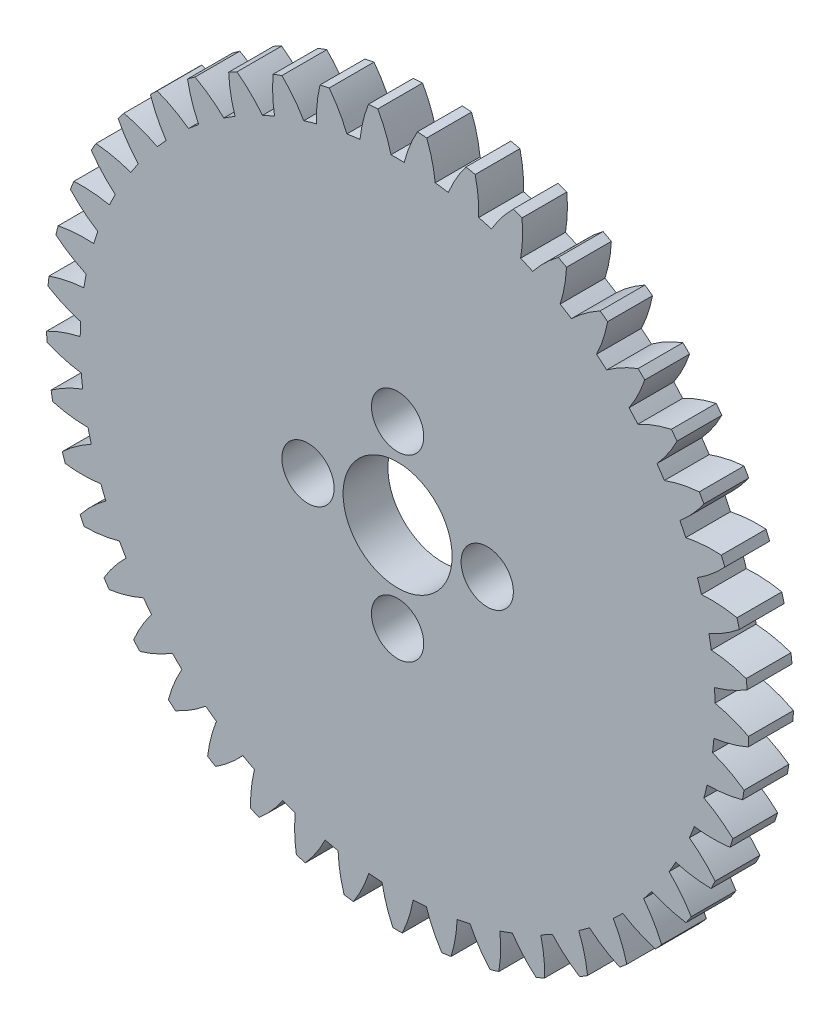
SolidWorks part; units mm, degrees
ref_plane "Front Plane" through (0, 0, 0) normal (0, 0, 1) x (1, 0, 0)
ref_plane "Top Plane" through (0, 0, 0) normal (0, 1, 0) x (1, 0, 0)
ref_plane "Right Plane" through (0, 0, 0) normal (1, 0, 0) x (0, 0, -1)
sketch "Model" plane through (0, 0, 0) normal (0, 0, 1) x (1, 0, 0)
  circle A0 centre (55.7791, 90.651) radius 15.95 construction
  arc A1 (32.4426, 93.4186) -> (32.3772, 92.7957) centre (55.7791, 90.651) ccw
  arc A2 (34.7806, 93.9041) -> (32.4426, 93.4186) centre (35.4255, 84.9273) ccw
  arc A3 (34.9343, 94.7759) -> (34.7806, 93.9041) centre (55.7791, 90.651) ccw
  arc A4 (32.9034, 96.0318) -> (34.9343, 94.7759) centre (38.6106, 102.9908) ccw
  arc A5 (33.0549, 96.6395) -> (32.9034, 96.0318) centre (55.7791, 90.651) ccw
  arc A6 (35.4377, 96.7949) -> (33.0549, 96.6395) centre (34.827, 87.8157) ccw
  arc A7 (35.7112, 97.6368) -> (35.4377, 96.7949) centre (55.7791, 90.651) ccw
  arc A8 (33.8749, 99.1631) -> (35.7112, 97.6368) centre (40.495, 105.2601) ccw
  arc A9 (34.1095, 99.7438) -> (33.8749, 99.1631) centre (55.7791, 90.651) ccw
  arc A10 (36.4907, 99.5661) -> (34.1095, 99.7438) centre (34.6363, 90.7592) ccw
  arc A11 (36.8788, 100.3617) -> (36.4907, 99.5661) centre (55.7791, 90.651) ccw
  arc A12 (35.2727, 102.1287) -> (36.8788, 100.3617) centre (42.677, 107.2451) ccw
  arc A13 (35.5859, 102.6711) -> (35.2727, 102.1287) centre (55.7791, 90.651) ccw
  arc A14 (37.9192, 102.1637) -> (35.5859, 102.6711) centre (34.8571, 93.7007) ccw
  arc A15 (38.4142, 102.8976) -> (37.9192, 102.1637) centre (55.7791, 90.651) ccw
  arc A16 (37.0697, 104.871) -> (38.4142, 102.8976) centre (45.1139, 108.907) ccw
  arc A17 (37.4553, 105.3645) -> (37.0697, 104.871) centre (55.7791, 90.651) ccw
  arc A18 (39.6953, 104.5373) -> (37.4553, 105.3645) centre (35.4852, 96.5828) ccw
  arc A19 (40.2876, 105.1951) -> (39.6953, 104.5373) centre (55.7791, 90.651) ccw
  arc A20 (39.2308, 107.3364) -> (40.2876, 105.1951) centre (47.7585, 110.2137) ccw
  arc A21 (39.6813, 107.7715) -> (39.2308, 107.3364) centre (55.7791, 90.651) ccw
  arc A22 (41.7844, 106.6406) -> (39.6813, 107.7715) centre (36.5082, 99.3494) ccw
  arc A23 (42.4625, 107.2096) -> (41.7844, 106.6406) centre (55.7791, 90.651) ccw
  arc A24 (41.714, 109.4771) -> (42.4625, 107.2096) centre (50.5591, 111.1395) ccw
  arc A25 (42.2207, 109.8452) -> (41.714, 109.4771) centre (55.7791, 90.651) ccw
  arc A26 (44.1459, 108.4327) -> (42.2207, 109.8452) centre (37.9063, 101.9467) ccw
  arc A27 (44.8966, 108.9018) -> (44.1459, 108.4327) centre (55.7791, 90.651) ccw
  arc A28 (44.471, 111.2514) -> (44.8966, 108.9018) centre (53.4614, 111.6666) ccw
  arc A29 (45.024, 111.5454) -> (44.471, 111.2514) centre (55.7791, 90.651) ccw
  arc A30 (46.7339, 109.8787) -> (45.024, 111.5454) centre (39.6523, 104.3242) ccw
  arc A31 (47.5425, 110.2387) -> (46.7339, 109.8787) centre (55.7791, 90.651) ccw
  arc A32 (47.4481, 112.6247) -> (47.5425, 110.2387) centre (56.4088, 111.7847) ccw
  arc A33 (48.0366, 112.8389) -> (47.4481, 112.6247) centre (55.7791, 90.651) ccw
  arc A34 (49.4979, 110.9504) -> (48.0366, 112.8389) centre (41.7122, 106.4356) ccw
  arc A35 (50.3488, 111.1944) -> (49.4979, 110.9504) centre (55.7791, 90.651) ccw
  arc A36 (50.5873, 113.5703) -> (50.3488, 111.1944) centre (59.3439, 111.4914) ccw
  arc A37 (51.1999, 113.7005) -> (50.5873, 113.5703) centre (55.7791, 90.651) ccw
  arc A38 (52.3842, 111.627) -> (51.1999, 113.7005) centre (44.0459, 108.2397) ccw
  arc A39 (53.2607, 111.7502) -> (52.3842, 111.627) centre (55.7791, 90.651) ccw
  arc A40 (53.8276, 114.0698) -> (53.2607, 111.7502) centre (62.2096, 110.7924) ccw
  arc A41 (54.4524, 114.1135) -> (53.8276, 114.0698) centre (55.7791, 90.651) ccw
  arc A42 (55.3365, 111.8954) -> (54.4524, 114.1135) centre (46.608, 109.7014) ccw
  arc A43 (56.2217, 111.8954) -> (55.3365, 111.8954) centre (55.7791, 90.651) ccw
  arc A44 (57.1058, 114.1135) -> (56.2217, 111.8954) centre (64.9502, 109.7014) ccw
  arc A45 (57.7306, 114.0698) -> (57.1058, 114.1135) centre (55.7791, 90.651) ccw
  arc A46 (58.2975, 111.7502) -> (57.7306, 114.0698) centre (49.3486, 110.7924) ccw
  arc A47 (59.174, 111.627) -> (58.2975, 111.7502) centre (55.7791, 90.651) ccw
  arc A48 (60.3583, 113.7005) -> (59.174, 111.627) centre (67.5123, 108.2397) ccw
  arc A49 (60.9709, 113.5703) -> (60.3583, 113.7005) centre (55.7791, 90.651) ccw
  arc A50 (61.2094, 111.1944) -> (60.9709, 113.5703) centre (52.2143, 111.4914) ccw
  arc A51 (62.0603, 110.9504) -> (61.2094, 111.1944) centre (55.7791, 90.651) ccw
  arc A52 (63.5216, 112.8389) -> (62.0603, 110.9504) centre (69.8459, 106.4356) ccw
  arc A53 (64.1101, 112.6247) -> (63.5216, 112.8389) centre (55.7791, 90.651) ccw
  arc A54 (64.0156, 110.2387) -> (64.1101, 112.6247) centre (55.1494, 111.7847) ccw
  arc A55 (64.8243, 109.8787) -> (64.0156, 110.2387) centre (55.7791, 90.651) ccw
  arc A56 (66.5342, 111.5454) -> (64.8243, 109.8787) centre (71.9058, 104.3242) ccw
  arc A57 (67.0872, 111.2514) -> (66.5342, 111.5454) centre (55.7791, 90.651) ccw
  arc A58 (66.6616, 108.9018) -> (67.0872, 111.2514) centre (58.0968, 111.6666) ccw
  arc A59 (67.4122, 108.4327) -> (66.6616, 108.9018) centre (55.7791, 90.651) ccw
  arc A60 (69.3375, 109.8452) -> (67.4122, 108.4327) centre (73.6518, 101.9467) ccw
  arc A61 (69.8442, 109.4771) -> (69.3375, 109.8452) centre (55.7791, 90.651) ccw
  arc A62 (69.0957, 107.2096) -> (69.8442, 109.4771) centre (60.999, 111.1395) ccw
  arc A63 (69.7738, 106.6406) -> (69.0957, 107.2096) centre (55.7791, 90.651) ccw
  arc A64 (71.8768, 107.7715) -> (69.7738, 106.6406) centre (75.05, 99.3494) ccw
  arc A65 (72.3274, 107.3364) -> (71.8768, 107.7715) centre (55.7791, 90.651) ccw
  arc A66 (71.2706, 105.1951) -> (72.3274, 107.3364) centre (63.7997, 110.2137) ccw
  arc A67 (71.8629, 104.5373) -> (71.2706, 105.1951) centre (55.7791, 90.651) ccw
  arc A68 (74.1029, 105.3645) -> (71.8629, 104.5373) centre (76.073, 96.5828) ccw
  arc A69 (74.4885, 104.871) -> (74.1029, 105.3645) centre (55.7791, 90.651) ccw
  arc A70 (73.144, 102.8976) -> (74.4885, 104.871) centre (66.4442, 108.907) ccw
  arc A71 (73.639, 102.1637) -> (73.144, 102.8976) centre (55.7791, 90.651) ccw
  arc A72 (75.9723, 102.6711) -> (73.639, 102.1637) centre (76.7011, 93.7007) ccw
  arc A73 (76.2855, 102.1287) -> (75.9723, 102.6711) centre (55.7791, 90.651) ccw
  arc A74 (74.6794, 100.3617) -> (76.2855, 102.1287) centre (68.8812, 107.2451) ccw
  arc A75 (75.0674, 99.5661) -> (74.6794, 100.3617) centre (55.7791, 90.651) ccw
  arc A76 (77.4487, 99.7438) -> (75.0674, 99.5661) centre (76.9219, 90.7592) ccw
  arc A77 (77.6833, 99.1631) -> (77.4487, 99.7438) centre (55.7791, 90.651) ccw
  arc A78 (75.8469, 97.6368) -> (77.6833, 99.1631) centre (71.0632, 105.2601) ccw
  arc A79 (76.1205, 96.7949) -> (75.8469, 97.6368) centre (55.7791, 90.651) ccw
  arc A80 (78.5033, 96.6395) -> (76.1205, 96.7949) centre (76.7312, 87.8157) ccw
  arc A81 (78.6548, 96.0318) -> (78.5033, 96.6395) centre (55.7791, 90.651) ccw
  arc A82 (76.6239, 94.7759) -> (78.6548, 96.0318) centre (72.9476, 102.9908) ccw
  arc A83 (76.7776, 93.9041) -> (76.6239, 94.7759) centre (55.7791, 90.651) ccw
  arc A84 (79.1155, 93.4186) -> (76.7776, 93.9041) centre (76.1327, 84.9273) ccw
  arc A85 (79.181, 92.7957) -> (79.1155, 93.4186) centre (55.7791, 90.651) ccw
  arc A86 (76.9951, 91.8347) -> (79.181, 92.7957) centre (74.4979, 100.4813) ccw
  arc A87 (77.026, 90.9501) -> (76.9951, 91.8347) centre (55.7791, 90.651) ccw
  arc A88 (79.2736, 90.1439) -> (77.026, 90.9501) centre (75.138, 82.1503) ccw
  arc A89 (79.2518, 89.5179) -> (79.2736, 90.1439) centre (55.7791, 90.651) ccw
  arc A90 (76.9534, 88.8705) -> (79.2518, 89.5179) centre (75.6839, 97.7805) ccw
  arc A91 (76.8608, 87.9902) -> (76.9534, 88.8705) centre (55.7791, 90.651) ccw
  arc A92 (78.9744, 86.879) -> (76.8608, 87.9902) centre (73.7666, 79.5388) ccw
  arc A93 (78.8656, 86.2622) -> (78.9744, 86.879) centre (55.7791, 90.651) ccw
  arc A94 (76.4995, 85.9409) -> (78.8656, 86.2622) centre (76.4824, 94.9409) ccw
  arc A95 (76.2854, 85.082) -> (76.4995, 85.9409) centre (55.7791, 90.651) ccw
  arc A96 (78.2237, 83.6875) -> (76.2854, 85.082) centre (72.045, 77.1436) ccw
  arc A97 (78.0302, 83.0919) -> (78.2237, 83.6875) centre (55.7791, 90.651) ccw
  arc A98 (75.6423, 83.103) -> (78.0302, 83.0919) centre (76.8779, 92.0178) ccw
  arc A99 (75.3107, 82.2823) -> (75.6423, 83.103) centre (55.7791, 90.651) ccw
  arc A100 (77.0362, 80.6316) -> (75.3107, 82.2823) centre (70.0068, 75.0112) ccw
  arc A101 (76.7616, 80.0687) -> (77.0362, 80.6316) centre (55.7791, 90.651) ccw
  arc A102 (74.3986, 80.4121) -> (76.7616, 80.0687) centre (76.8628, 89.0681) ccw
  arc A103 (73.956, 79.6455) -> (74.3986, 80.4121) centre (55.7791, 90.651) ccw
  arc A104 (75.4349, 77.7707) -> (73.956, 79.6455) centre (67.6917, 73.1833) ccw
  arc A105 (75.0846, 77.2515) -> (75.4349, 77.7707) centre (55.7791, 90.651) ccw
  arc A106 (72.7924, 77.9204) -> (75.0846, 77.2515) centre (76.4374, 86.1492) ccw
  arc A107 (72.2474, 77.2228) -> (72.7924, 77.9204) centre (55.7791, 90.651) ccw
  arc A108 (73.451, 75.1605) -> (72.2474, 77.2228) centre (65.1448, 71.6954) ccw
  arc A109 (73.0319, 74.6951) -> (73.451, 75.1605) centre (55.7791, 90.651) ccw
  arc A110 (70.8551, 75.6765) -> (73.0319, 74.6951) centre (75.6098, 83.318) ccw
  arc A111 (70.2183, 75.0616) -> (70.8551, 75.6765) centre (55.7791, 90.651) ccw
  arc A112 (71.1231, 72.8518) -> (70.2183, 75.0616) centre (62.4155, 70.5764) ccw
  arc A113 (70.6434, 72.4492) -> (71.1231, 72.8518) centre (55.7791, 90.651) ccw
  arc A114 (68.6243, 73.724) -> (70.6434, 72.4492) centre (74.3963, 80.6294) ccw
  arc A115 (67.9082, 73.2037) -> (68.6243, 73.724) centre (55.7791, 90.651) ccw
  arc A116 (68.4967, 70.8895) -> (67.9082, 73.2037) centre (59.5571, 69.8482) ccw
  arc A117 (67.9655, 70.5577) -> (68.4967, 70.8895) centre (55.7791, 90.651) ccw
  arc A118 (66.1435, 72.1011) -> (67.9655, 70.5577) centre (72.8203, 78.136) ccw
  arc A119 (65.3619, 71.6855) -> (66.1435, 72.1011) centre (55.7791, 90.651) ccw
  arc A120 (65.6226, 69.3119) -> (65.3619, 71.6855) centre (56.6252, 69.5248) ccw
  arc A121 (65.0505, 69.0572) -> (65.6226, 69.3119) centre (55.7791, 90.651) ccw
  arc A122 (63.461, 70.8391) -> (65.0505, 69.0572) centre (70.9128, 75.8861) ccw
  arc A123 (62.6292, 70.5364) -> (63.461, 70.8391) centre (55.7791, 90.651) ccw
  arc A124 (62.557, 68.1496) -> (62.6292, 70.5364) centre (53.6767, 69.6127) ccw
  arc A125 (61.955, 67.977) -> (62.557, 68.1496) centre (55.7791, 90.651) ccw
  arc A126 (60.629, 69.9628) -> (61.955, 67.977) centre (68.7106, 73.9236) ccw
  arc A127 (59.7631, 69.7788) -> (60.629, 69.9628) centre (55.7791, 90.651) ccw
  arc A128 (59.3595, 67.4253) -> (59.7631, 69.7788) centre (50.7692, 70.11) ccw
  arc A129 (58.7393, 67.3381) -> (59.3595, 67.4253) centre (55.7791, 90.651) ccw
  arc A130 (57.7025, 69.4892) -> (58.7393, 67.3381) centre (66.2567, 72.2866) ccw
  arc A131 (56.8195, 69.4274) -> (57.7025, 69.4892) centre (55.7791, 90.651) ccw
  arc A132 (56.0922, 67.1531) -> (56.8195, 69.4274) centre (47.9592, 71.0071) ccw
  arc A133 (55.4659, 67.1531) -> (56.0922, 67.1531) centre (55.7791, 90.651) ccw
  arc A134 (54.7387, 69.4274) -> (55.4659, 67.1531) centre (63.599, 71.0071) ccw
  arc A135 (53.8556, 69.4892) -> (54.7387, 69.4274) centre (55.7791, 90.651) ccw
  arc A136 (52.8189, 67.3381) -> (53.8556, 69.4892) centre (45.3014, 72.2866) ccw
  arc A137 (52.1987, 67.4253) -> (52.8189, 67.3381) centre (55.7791, 90.651) ccw
  arc A138 (51.7951, 69.7788) -> (52.1987, 67.4253) centre (60.789, 70.11) ccw
  arc A139 (50.9292, 69.9628) -> (51.7951, 69.7788) centre (55.7791, 90.651) ccw
  arc A140 (49.6032, 67.977) -> (50.9292, 69.9628) centre (42.8476, 73.9236) ccw
  arc A141 (49.0012, 68.1496) -> (49.6032, 67.977) centre (55.7791, 90.651) ccw
  arc A142 (48.929, 70.5364) -> (49.0012, 68.1496) centre (57.8815, 69.6127) ccw
  arc A143 (48.0972, 70.8391) -> (48.929, 70.5364) centre (55.7791, 90.651) ccw
  arc A144 (46.5077, 69.0572) -> (48.0972, 70.8391) centre (40.6454, 75.8861) ccw
  arc A145 (45.9355, 69.3119) -> (46.5077, 69.0572) centre (55.7791, 90.651) ccw
  arc A146 (46.1962, 71.6855) -> (45.9355, 69.3119) centre (54.933, 69.5248) ccw
  arc A147 (45.4147, 72.1011) -> (46.1962, 71.6855) centre (55.7791, 90.651) ccw
  arc A148 (43.5927, 70.5577) -> (45.4147, 72.1011) centre (38.7378, 78.136) ccw
  arc A149 (43.0615, 70.8895) -> (43.5927, 70.5577) centre (55.7791, 90.651) ccw
  arc A150 (43.65, 73.2037) -> (43.0615, 70.8895) centre (52.0011, 69.8482) ccw
  arc A151 (42.9339, 73.724) -> (43.65, 73.2037) centre (55.7791, 90.651) ccw
  arc A152 (40.9148, 72.4492) -> (42.9339, 73.724) centre (37.1619, 80.6294) ccw
  arc A153 (40.435, 72.8518) -> (40.9148, 72.4492) centre (55.7791, 90.651) ccw
  arc A154 (41.3399, 75.0616) -> (40.435, 72.8518) centre (49.1426, 70.5764) ccw
  arc A155 (40.7031, 75.6765) -> (41.3399, 75.0616) centre (55.7791, 90.651) ccw
  arc A156 (38.5263, 74.6951) -> (40.7031, 75.6765) centre (35.9484, 83.318) ccw
  arc A157 (38.1072, 75.1605) -> (38.5263, 74.6951) centre (55.7791, 90.651) ccw
  arc A158 (39.3108, 77.2228) -> (38.1072, 75.1605) centre (46.4134, 71.6954) ccw
  arc A159 (38.7658, 77.9204) -> (39.3108, 77.2228) centre (55.7791, 90.651) ccw
  arc A160 (36.4736, 77.2515) -> (38.7658, 77.9204) centre (35.1208, 86.1492) ccw
  arc A161 (36.1233, 77.7707) -> (36.4736, 77.2515) centre (55.7791, 90.651) ccw
  arc A162 (37.6022, 79.6455) -> (36.1233, 77.7707) centre (43.8664, 73.1833) ccw
  arc A163 (37.1596, 80.4121) -> (37.6022, 79.6455) centre (55.7791, 90.651) ccw
  arc A164 (34.7966, 80.0687) -> (37.1596, 80.4121) centre (34.6953, 89.0681) ccw
  arc A165 (34.522, 80.6316) -> (34.7966, 80.0687) centre (55.7791, 90.651) ccw
  arc A166 (36.2474, 82.2823) -> (34.522, 80.6316) centre (41.5513, 75.0112) ccw
  arc A167 (35.9158, 83.103) -> (36.2474, 82.2823) centre (55.7791, 90.651) ccw
  arc A168 (33.528, 83.0919) -> (35.9158, 83.103) centre (34.6802, 92.0178) ccw
  arc A169 (33.3345, 83.6875) -> (33.528, 83.0919) centre (55.7791, 90.651) ccw
  arc A170 (35.2728, 85.082) -> (33.3345, 83.6875) centre (39.5132, 77.1436) ccw
  arc A171 (35.0587, 85.9409) -> (35.2728, 85.082) centre (55.7791, 90.651) ccw
  arc A172 (32.6925, 86.2622) -> (35.0587, 85.9409) centre (35.0758, 94.9409) ccw
  arc A173 (32.5838, 86.879) -> (32.6925, 86.2622) centre (55.7791, 90.651) ccw
  arc A174 (34.6973, 87.9902) -> (32.5838, 86.879) centre (37.7916, 79.5388) ccw
  arc A175 (34.6048, 88.8705) -> (34.6973, 87.9902) centre (55.7791, 90.651) ccw
  arc A176 (32.3064, 89.5179) -> (34.6048, 88.8705) centre (35.8743, 97.7805) ccw
  arc A177 (32.2846, 90.1439) -> (32.3064, 89.5179) centre (55.7791, 90.651) ccw
  arc A178 (34.5322, 90.9501) -> (32.2846, 90.1439) centre (36.4201, 82.1503) ccw
  arc A179 (34.5631, 91.8347) -> (34.5322, 90.9501) centre (55.7791, 90.651) ccw
  arc A180 (32.3772, 92.7957) -> (34.5631, 91.8347) centre (37.0603, 100.4813) ccw
extrude "Boss-Extrude1" add sketch "Model" along normal blind 3
sketch "Sketch2" plane through (0, 0, 3) normal (0, 0, 1) x (1, 0, 0)
  circle A0 centre (55.7791, 90.651) radius 21.249 construction
  circle A1 centre (55.7791, 90.651) radius 3.65
  dimension "D1" = 7.3
extrude "Cut-Extrude1" cut sketch "Sketch2" against normal blind 3
sketch "Sketch3" plane through (0, 0, 3) normal (0, 0, 1) x (1, 0, 0)
  line L0 (55.7791, 90.651) -> (61.7791, 90.651) construction
  circle A0 centre (61.7791, 90.651) radius 1.75
  dimension "D1" = 3.5
  dimension "D2" = 6
extrude "Cut-Extrude2" cut sketch "Sketch3" against normal blind 3
pattern_circular "CirPattern1" count 4 over 360 about axis through (55.7791, 90.651, 0) along (0, 0, 1) of "Cut-Extrude2"
sketch "Sketch6" plane through (0, 0, 0) normal (0, 0, 1) x (1, 0, 0)
  circle A0 centre (55.7791, 90.651) radius 22.5 construction
  dimension "D1" = 45
